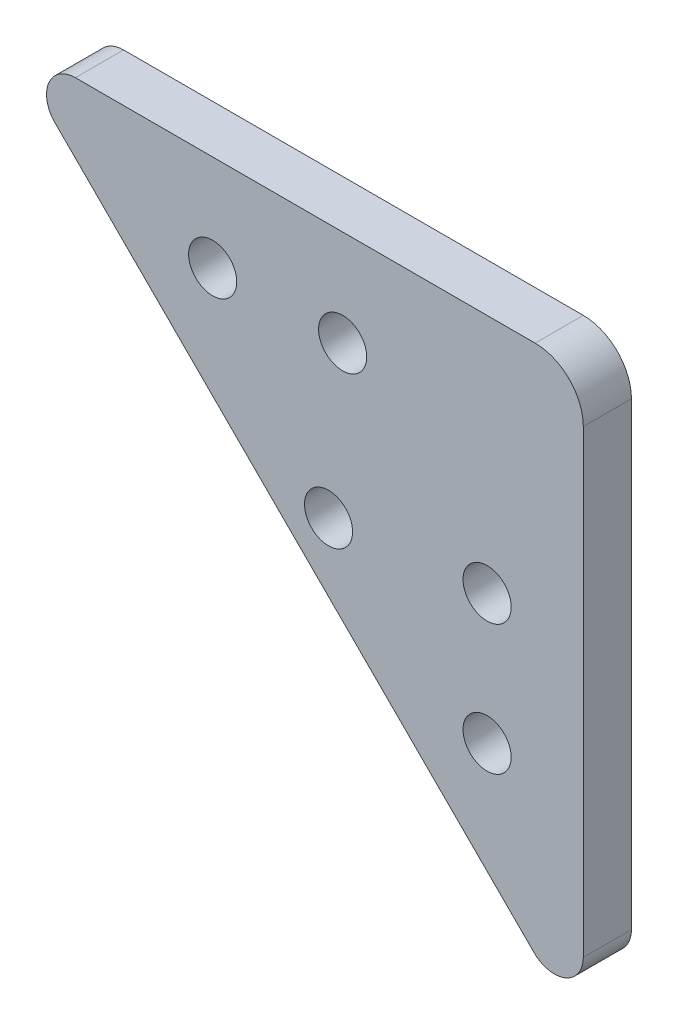
SolidWorks part; units mm, degrees
ref_plane "Front Plane" through (0, 0, 0) normal (0, 0, 1) x (1, 0, 0)
ref_plane "Top Plane" through (0, 0, 0) normal (0, 1, 0) x (1, 0, 0)
ref_plane "Right Plane" through (0, 0, 0) normal (1, 0, 0) x (0, 0, -1)
sketch "Sketch1" plane through (0, 0, 0) normal (0, 0, 1) x (1, 0, 0)
  line L0 (-22.7574, 30) -> (25, 30)
  line L1 (30, 25) -> (30, -22.7574)
  line L2 (24.8787, -24.8787) -> (-24.8787, 24.8787)
  line L3 (-22.7574, 27) -> (30, 1.1213) construction
  line L4 (27, -22.7574) -> (1.1213, 30) construction
  line L5 (0, 0) -> (25, 25) construction
  arc A0 (25, 30) -> (30, 25) centre (25, 25) cw
  arc A1 (-22.7574, 30) -> (-24.8787, 24.8787) centre (-22.7574, 27) ccw
  arc A2 (30, -22.7574) -> (24.8787, -24.8787) centre (27, -22.7574) cw
  circle A3 centre (5, 20.0064) radius 2.5
  circle A4 centre (-8.5, 20.0064) radius 2.5
  circle A5 centre (20.0064, 5) radius 2.5
  circle A6 centre (20.0064, -8.5) radius 2.5
  circle A7 centre (3.5355, 3.5355) radius 2.5
  point P6 (30, 30)
  point P9 (-30, 30)
  dimension "D5" = 5
  dimension "D6" = 3
  dimension "D7" = 25
  dimension "D8" = 13.5
  dimension "D9" = 5
  dimension "D10" = 5
  dimension "D11" = 5
  dimension "D1" = 45
  dimension "D2" = 60
  dimension "D3" = 30
  dimension "D4" = 30
  dimension "D12" = 5
extrude "Boss-Extrude2" add sketch "Sketch1" along normal blind 5
